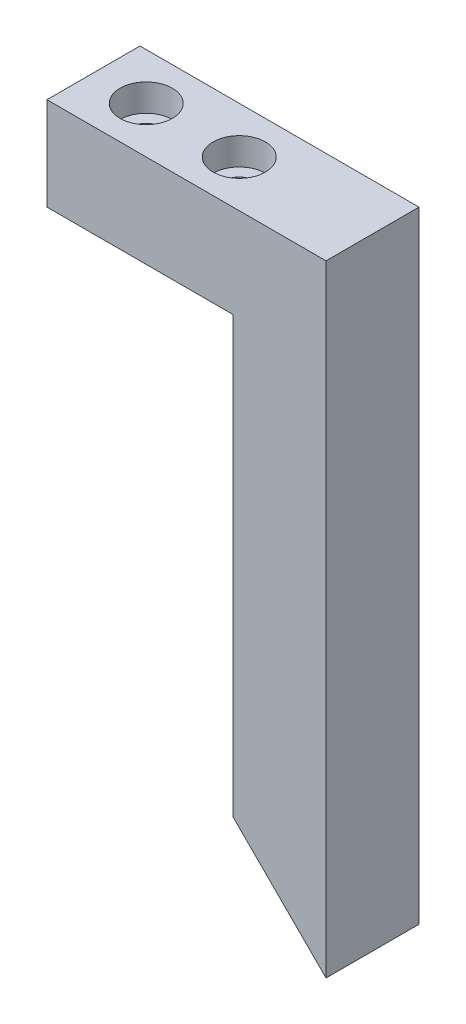
SolidWorks part; units mm, degrees
ref_plane "Front" through (0, 0, 0) normal (0, 0, 1) x (1, 0, 0)
ref_plane "Top" through (0, 0, 0) normal (0, 1, 0) x (1, 0, 0)
ref_plane "Right" through (0, 0, 0) normal (1, 0, 0) x (0, 0, -1)
sketch "Sketch1" plane through (0, 0, 0) normal (0, 0, 1) x (1, 0, 0)
  line L1 (0, 0) -> (38.1, 0)
  line L2 (0, 0) -> (0, -84.8)
  line L3 (0, -84.8) -> (38.1, -84.8)
  line L4 (38.1, 0) -> (38.1, -84.8)
  dimension "D1" = 84.8
  dimension "D2" = 38.1
extrude "Boss-Extrude1" add sketch "Sketch1" along normal mid plane 12.7
sketch "Sketch2" plane through (0, 0, 6.35) normal (0, 0, 1) x (1, 0, 0)
  line L0 (38.1, 0) -> (0, 0) construction
  line L1 (0, -84.8) -> (25.4, -84.8)
  line L2 (0, -84.8) -> (0, -12.7)
  line L3 (0, -12.7) -> (25.4, -12.7)
  line L4 (25.4, -84.8) -> (25.4, -12.7)
  dimension "D1" = 25.4
  dimension "D2" = 12.7
extrude "Cut-Extrude1" cut sketch "Sketch2" against normal through all
hole_wizard "CBORE for #6 Socket Head Cap Screw1" positions "Sketch8" profile "Sketch7" counterbore size "#6" standard "Ansi Inch" end condition through all
sketch "Sketch8" plane through (0, 0, 0) normal (0, 1, 0) x (-1, 0, 0)
  line L0 (50, 0) -> (-50, 0) construction
  line L1 (0, 6.35) -> (0, -6.35) construction
  point P0 (-7.2, 0)
  point P1 (-19.9, 0)
  dimension "D1" = 7.2
  dimension "D2" = 12.7
sketch "Sketch7" plane through (7.2, 0, 0) normal (1, 0, 0) x (0, 0, 1)
  line L0 (0, 0) -> (0, 84.8)
  line L1 (0, 84.8) -> (1.8986, 84.8)
  line L3 (1.8986, 84.8) -> (1.8987, 3.7052)
  line L4 (1.8987, 3.7052) -> (3.5725, 3.7052)
  line L5 (3.5725, 3.7052) -> (3.5725, 0)
  line L7 (3.5725, 0) -> (0, 0)
  line L11 (0, -6.35) -> (0, 107.95) construction
  dimension "Thru Hole Dia." = 3.7973
  dimension "Thru Hole Depth" = 84.8
  dimension "C'Bore Dia." = 7.145
  dimension "C'Bore Depth" = 3.7052
sketch "Sketch9" plane through (0, 0, 6.35) normal (0, 0, 1) x (1, 0, 0)
  line L0 (38.1, -84.8) -> (24.4, -71.1)
  line L1 (24.4, -71.1) -> (24.4, -85.8)
  line L2 (24.4, -85.8) -> (38.1, -85.8)
  line L3 (38.1, -85.8) -> (38.1, -84.8)
  line L4 (25.4, -84.8) -> (38.1, -84.8) construction
  line L5 (25.4, -84.8) -> (25.4, -12.7) construction
  dimension "D1" = 45
  dimension "D2" = 1
  dimension "D3" = 1
extrude "Cut-Extrude2" cut sketch "Sketch9" against normal through all
hole_wizard "#4-40 Tapped Hole2" positions "Sketch13" profile "Sketch12" tap size "#4-40" standard "ANSI Inch"
sketch "Sketch13" plane through (-23.35, -23.35, 0) normal (-0.7071, -0.7071, 0) x (-0.7071, 0.7071, 0)
  line L0 (-68.9429, 0) -> (-86.9034, 0) construction
  line L1 (-68.9429, 6.35) -> (-68.9429, -6.35) construction
  line L2 (-86.9034, -6.35) -> (-86.9034, 6.35) construction
  line L5 (-77.9232, 0) -> (-77.9232, 6.35) construction
  line L6 (-86.9034, 6.35) -> (-68.9429, 6.35) construction
  point P0 (-77.9232, 3.175)
  point P2 (-77.9232, -3.175)
sketch "Sketch12" plane through (31.75, -78.45, -3.175) normal (0, 0, 1) x (0.7071, -0.7071, 0)
  line L0 (0, 0) -> (0, 8.2692)
  line L1 (0, 8.2692) -> (1.1303, 7.59)
  line L2 (1.1303, 7.59) -> (1.1303, 0)
  line L5 (1.1303, 0) -> (0, 0)
  line L10 (0, 8.2692) -> (-1.1303, 7.59) construction
  line L11 (0, -6.35) -> (0, 107.95) construction
  dimension "Tap Drill Dia." = 2.2606
  dimension "Tap Drill Depth" = 7.59
  dimension "Drill Angle" = 118
cosmetic thread "Hole Thread3" parameters "D1"=5.69, "D2"=2.8448
cosmetic thread "Hole Thread4" parameters "D1"=5.69, "D2"=2.8448
